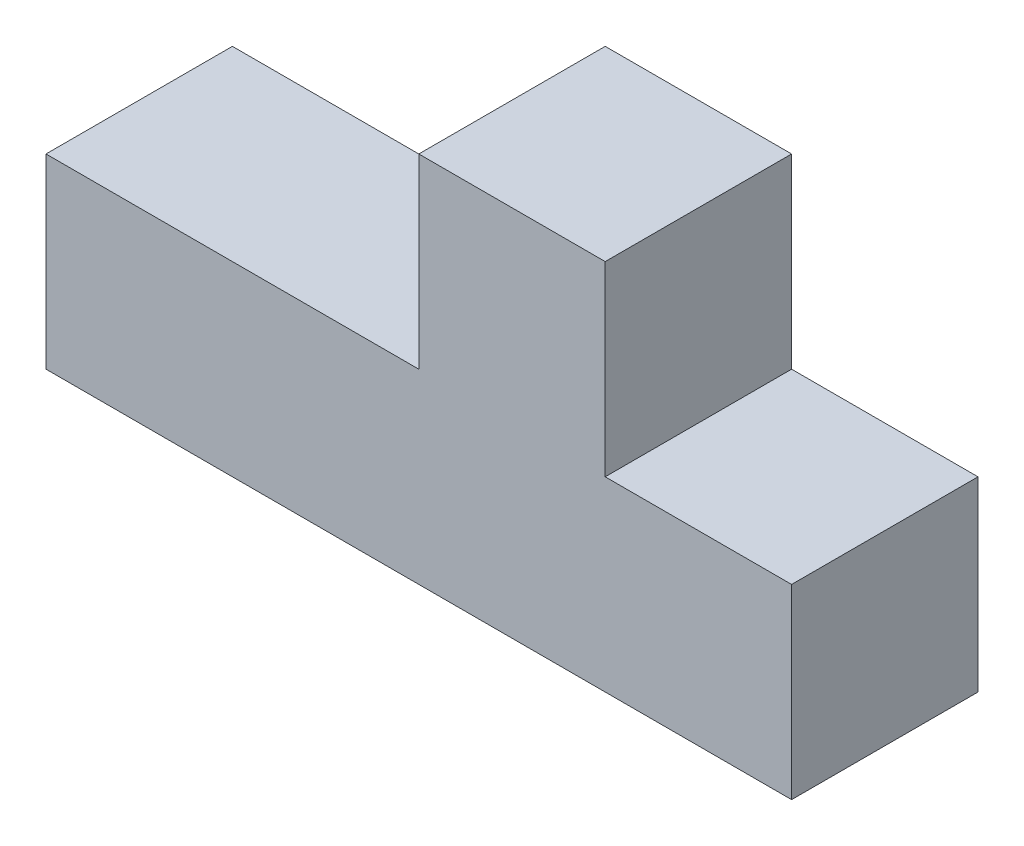
SolidWorks part; units mm, degrees
ref_plane "Front Plane" through (0, 0, 0) normal (0, 0, 1) x (1, 0, 0)
ref_plane "Top Plane" through (0, 0, 0) normal (0, 1, 0) x (1, 0, 0)
ref_plane "Right Plane" through (0, 0, 0) normal (1, 0, 0) x (0, 0, -1)
sketch "Sketch1" plane through (0, 0, 0) normal (0, 0, 1) x (1, 0, 0)
  line L0 (0, 0) -> (101.6, 0)
  line L1 (101.6, 0) -> (101.6, 25.4)
  line L2 (101.6, 25.4) -> (76.2, 25.4)
  line L3 (76.2, 25.4) -> (76.2, 50.8)
  line L4 (76.2, 50.8) -> (50.8, 50.8)
  line L5 (50.8, 50.8) -> (50.8, 25.4)
  line L6 (50.8, 25.4) -> (0, 25.4)
  line L7 (0, 25.4) -> (0, 0)
extrude "Boss-Extrude1" add sketch "Sketch1" along normal blind 25.4
